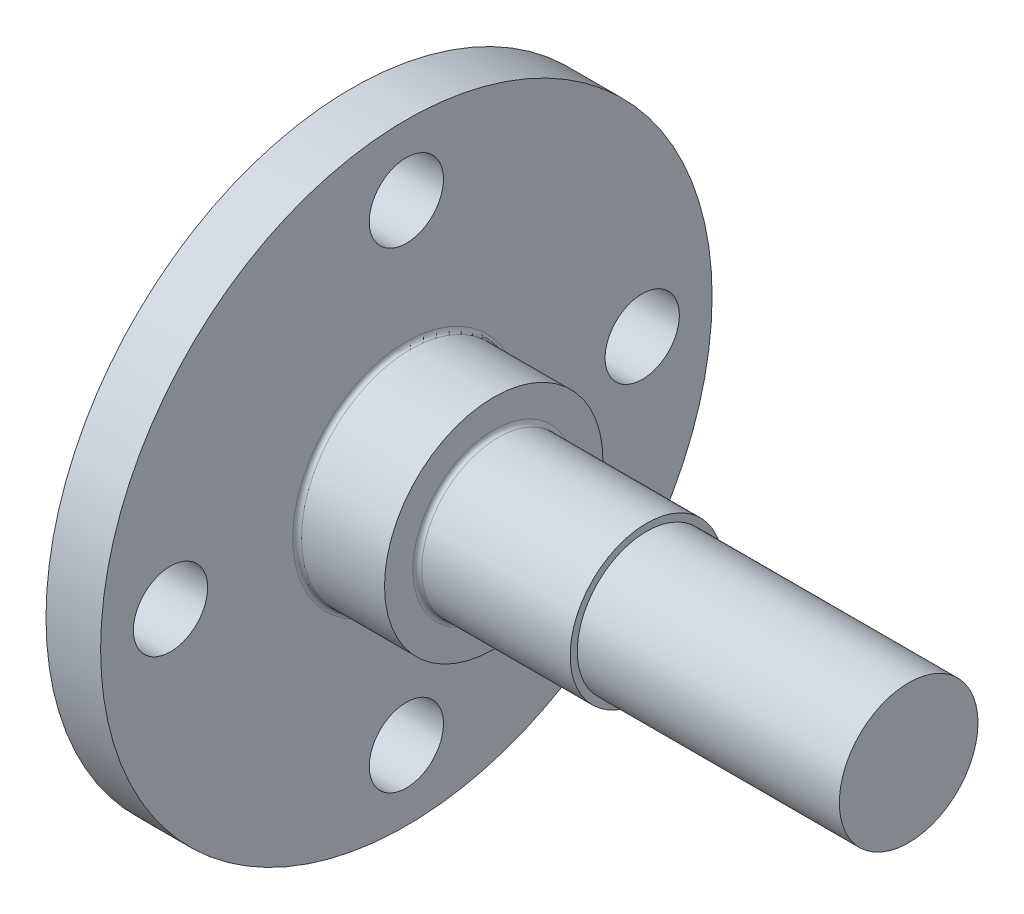
SolidWorks part; units mm, degrees
material "1060 Alloy"
ref_plane "Front" through (0, 0, 0) normal (0, 0, 1) x (1, 0, 0)
ref_plane "Top" through (0, 0, 0) normal (0, 1, 0) x (1, 0, 0)
ref_plane "Right" through (0, 0, 0) normal (1, 0, 0) x (0, 0, -1)
sketch "Sketch1" plane through (0, 0, 0) normal (1, 0, 0) x (0, 0, -1)
  line L1 (0, 0) -> (-120, 0)
  line L2 (0, 0) -> (0, 34)
  line L3 (0, 34) -> (-120, 34)
  line L4 (-120, 0) -> (-120, 34)
  dimension "D1" = 34
  dimension "D2" = 120
extrude "Boss-Extrude1" add sketch "Sketch1" along normal blind 5
sketch "Sketch2" plane through (5, 0, 0) normal (1, 0, 0) x (0, 0, -1)
  line L0 (-60, 34) -> (-60, 0)
  line L1 (0, 34) -> (-120, 34) construction
  line L2 (0, 0) -> (-120, 0) construction
  circle A0 centre (-60, 17) radius 5
  dimension "D1" = 10
extrude "Boss-Extrude2" add sketch "Sketch2" along normal blind 4 contours L0 A0 | L0 A0
sketch "Sketch3" plane through (9, 0, 0) normal (1, 0, 0) x (0, 0, -1)
  circle A0 centre (-60, 17) radius 3.5
  dimension "D1" = 7
extrude "Boss-Extrude3" add sketch "Sketch3" along normal blind 19
sketch "Sketch4" plane through (28, 0, 0) normal (1, 0, 0) x (0, 0, -1)
  circle A0 centre (-60, 17) radius 3.5
  circle A1 centre (-60, 17) radius 3.175
  dimension "D1" = 6.35
extrude "Cut-Extrude1" cut sketch "Sketch4" against normal blind 12
fillet "Fillet1" radius 0.2 2 edges at (9, 17, 56.5) (5, 17, 55)
sketch "Sketch5" plane through (5, 0, 0) normal (1, 0, 0) x (0, 0, -1)
  circle A0 centre (-60, 17) radius 14
  line M2 (-120, 34) -> (-120, 0)
  line M3 (-120, 0) -> (0, 0)
  line M4 (0, 0) -> (0, 34)
  line M5 (0, 34) -> (-120, 34)
  dimension "D1" = 28
extrude "Cut-Extrude2" cut sketch "Sketch5" against normal through all contours A0 M5 M2 M3 M4
hole_wizard "M3 Clearance Hole1" positions "Sketch7" profile "Sketch6" hole size "M3" standard "ISO"
sketch "Sketch7" plane through (5, 0, 0) normal (1, 0, 0) x (0, 0, -1)
  circle A0 centre (-60, 17) radius 14 construction
  point P0 (-60, 27.8)
  point P9 (-49.2, 17)
  point P10 (-60, 6.2)
  point P11 (-70.8, 17)
  dimension "D1" = 10.8
  dimension "D2" = 4
sketch "Sketch6" plane through (5, 27.8, 60) normal (0, 1, 0) x (0, 0, -1)
  line L0 (0, 0) -> (0, 16.0215)
  line L1 (0, 16.0215) -> (1.7, 15)
  line L2 (1.7, 15) -> (1.7, 0)
  line L5 (1.7, 0) -> (0, 0)
  line L10 (0, 16.0215) -> (-1.7, 15) construction
  line L11 (0, -6.35) -> (0, 107.95) construction
  dimension "Hole Dia." = 3.4
  dimension "Hole Depth" = 15
  dimension "Drill Angle" = 118
ref_plane "Plane1" through (0, 0, 46) normal (0, 0, -1) x (-1, 0, 0)
sketch "Sketch9" plane through (0, 0, 46) normal (0, 0, -1) x (-1, 0, 0)
  line L0 (0, 31) -> (-5, 31) construction
  line L1 (0, 3) -> (-2.5, 3)
  line L2 (0, 3) -> (0, 31)
  line L3 (0, 31) -> (-2.5, 31)
  line L4 (-2.5, 3) -> (-2.5, 31)
extrude "Cut-Extrude6" cut sketch "Sketch9" against normal through all contours L4 L1 L2 L3
